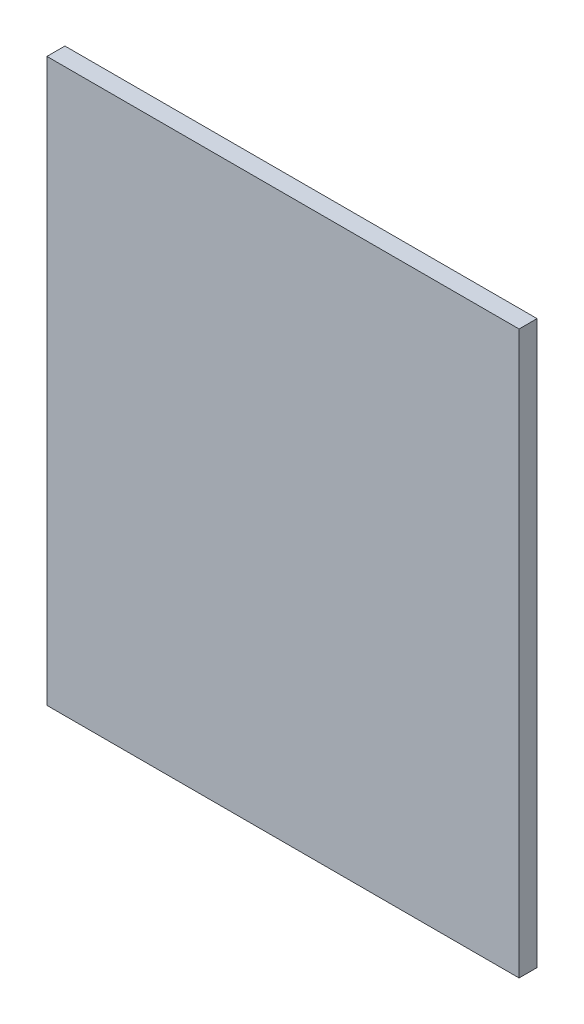
SolidWorks part; units mm, degrees
ref_plane "Front Plane" through (0, 0, 0) normal (0, 0, 1) x (1, 0, 0)
ref_plane "Top Plane" through (0, 0, 0) normal (0, 1, 0) x (1, 0, 0)
ref_plane "Right Plane" through (0, 0, 0) normal (1, 0, 0) x (0, 0, -1)
sketch "Sketch1" plane through (0, 0, 0) normal (0, 0, 1) x (1, 0, 0)
  line L1 (21, -25) -> (-21, -25)
  line L2 (21, -25) -> (21, 25)
  line L3 (21, 25) -> (-21, 25)
  line L4 (-21, -25) -> (-21, 25)
  line L5 (21, -25) -> (-21, 25) construction
  line L6 (21, 25) -> (-21, -25) construction
  point P0 (0, 0)
  dimension "D1" = 42
  dimension "D2" = 50
extrude "Boss-Extrude1" add sketch "Sketch1" along normal blind 1.6
